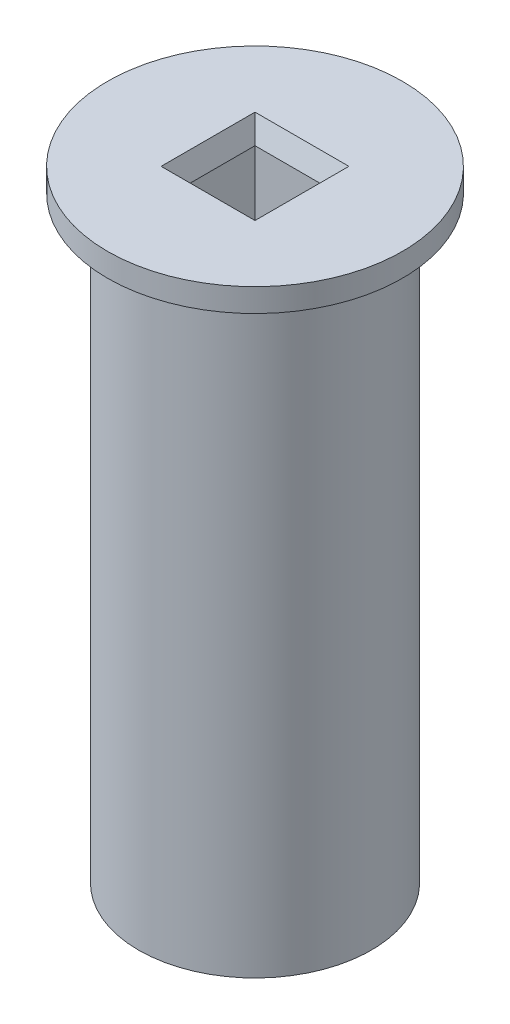
SolidWorks part; units mm, degrees
ref_plane "Спереди" through (0, 0, 0) normal (0, 0, 1) x (1, 0, 0)
ref_plane "Сверху" through (0, 0, 0) normal (0, 1, 0) x (1, 0, 0)
ref_plane "Справа" through (0, 0, 0) normal (1, 0, 0) x (0, 0, -1)
sketch "Эскиз1" plane through (0, 0, 0) normal (0, 1, 0) x (1, 0, 0)
  line L1 (5.05, -5.05) -> (-5.05, -5.05)
  line L2 (5.05, -5.05) -> (5.05, 5.05)
  line L3 (5.05, 5.05) -> (-5.05, 5.05)
  line L4 (-5.05, -5.05) -> (-5.05, 5.05)
  line L5 (5.05, -5.05) -> (-5.05, 5.05) construction
  line L6 (5.05, 5.05) -> (-5.05, -5.05) construction
  circle A0 centre (0, 0) radius 15
  dimension "D1" = 30
  dimension "D2" = 10.1
extrude "Бобышка-Вытянуть1" add sketch "Эскиз1" along normal blind 80
sketch "Sketch1" plane through (0, 80, 0) normal (0, 1, 0) x (1, 0, 0)
  line L1 (5.05, -5.05) -> (-5.05, -5.05)
  line L2 (5.05, -5.05) -> (5.05, 5.05)
  line L3 (5.05, 5.05) -> (-5.05, 5.05)
  line L4 (-5.05, -5.05) -> (-5.05, 5.05)
  line L5 (5.05, -5.05) -> (-5.05, 5.05) construction
  line L6 (5.05, 5.05) -> (-5.05, -5.05) construction
  circle A0 centre (0, 0) radius 19
  dimension "D1" = 38
extrude "Boss-Extrude1" add sketch "Sketch1" against normal blind 3
chamfer "Chamfer1" distance 1 angle 70 4 edges at (5.05, 80, 0) (0, 80, 5.05) (-5.05, 80, 0) (0, 80, -5.05)
